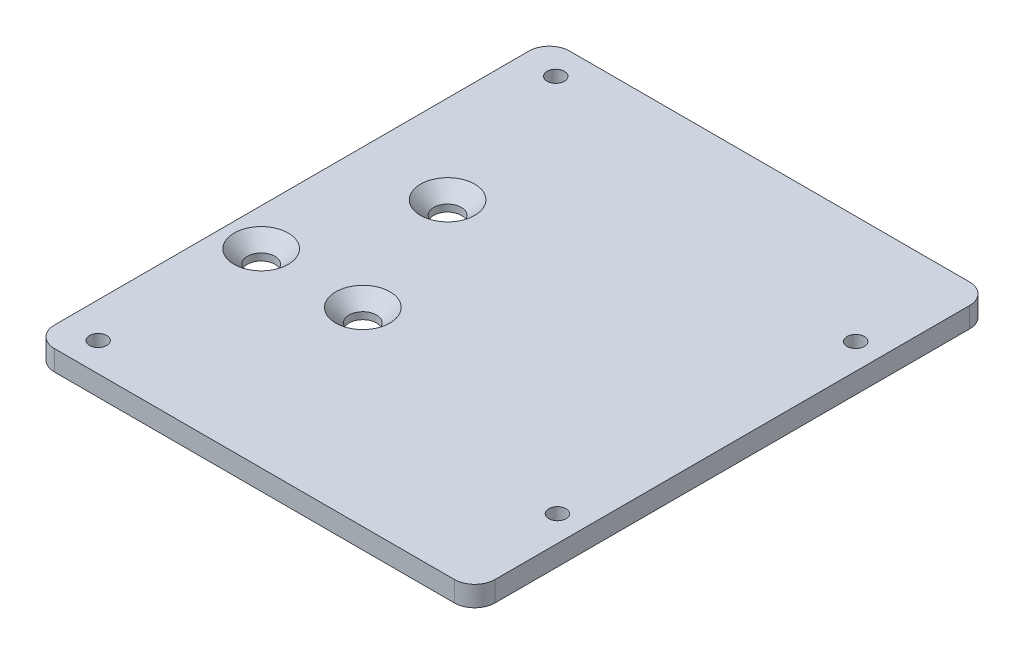
SolidWorks part; units mm, degrees
material "Thornel Mat VMA"
ref_plane "前视基准面" through (0, 0, 0) normal (0, 0, 1) x (1, 0, 0)
ref_plane "上视基准面" through (0, 0, 0) normal (0, 1, 0) x (1, 0, 0)
ref_plane "右视基准面" through (0, 0, 0) normal (1, 0, 0) x (0, 0, -1)
other "Configuration Table"
sketch "草图1" plane through (0, 0, 0) normal (0, 1, 0) x (1, 0, 0)
  line L1 (-32.5, -38) -> (32.5, -38)
  line L2 (-32.5, -38) -> (-32.5, 38)
  line L3 (-32.5, 38) -> (32.5, 38)
  line L4 (32.5, -38) -> (32.5, 38)
  line L5 (-32.5, -38) -> (32.5, 38) construction
  line L6 (-32.5, 38) -> (32.5, -38) construction
  point P0 (0, 0)
  dimension "D1" = 65
  dimension "D2" = 76
extrude "凸台-拉伸1" add sketch "草图1" along normal blind 3
fillet "圆角1" radius 3 4 edges at (-32.5, 1.5, 38) (-32.5, 1.5, -38) (32.5, 1.5, -38) (32.5, 1.5, 38)
sketch "草图3" plane through (0, 3, 0) normal (0, 1, 0) x (1, 0, 0)
  circle A0 centre (28.7, -22) radius 1.275
  circle A1 centre (28.7, 22) radius 1.275
  circle A2 centre (-27.3, 33.75) radius 1.275
  circle A3 centre (-27.3, -33.75) radius 1.275
  dimension "D1" = 2.55
extrude "切除-拉伸1" cut sketch "草图3" against normal through all both
sketch "草图6" plane through (0, 3, 0) normal (0, 1, 0) x (1, 0, 0)
  circle A0 centre (-27, -10) radius 2.025
  circle A1 centre (-12, -10) radius 2.025
  circle A2 centre (-19.5, 10) radius 2.025
  circle A3 centre (-12, -10) radius 2.025 construction
  circle A4 centre (-27, -10) radius 2.025 construction
  circle A5 centre (-19.5, 10) radius 2.025 construction
extrude "切除-拉伸3" cut sketch "草图6" against normal blind 10
hole_wizard "孔1" positions "3D草图1" profile "草图7" legacy end condition through all
sketch3d "3D草图1"
  line L0 (-12, 0, 10) -> (-12, 3, 10) construction
  line L1 (-27, 0, 10) -> (-27, 3, 10) construction
  line L2 (-19.5, 0, -10) -> (-19.5, 3, -10) construction
  point P0 (-12, 3, 10)
  point P4 (-27, 3, 10)
  point P8 (-19.5, 3, -10)
sketch "草图7" plane through (-12, 3, 10) normal (1, 0, 0) x (0, 0, 1)
  line L0 (0, 0) -> (0, 3)
  line L1 (0, 3) -> (2, 3)
  line L2 (2, 3) -> (2, 2)
  line L3 (2, 2) -> (4, 0)
  line L4 (4, 0) -> (0, 0)
  line L5 (0, -6.4453) -> (0, 115.525) construction
  line L6 (-2, 2) -> (-4, 0) construction
  dimension "直径" = 4
  dimension "深度" = 3
  dimension "锥坑角度" = 90
  dimension "锥坑直径" = 8
